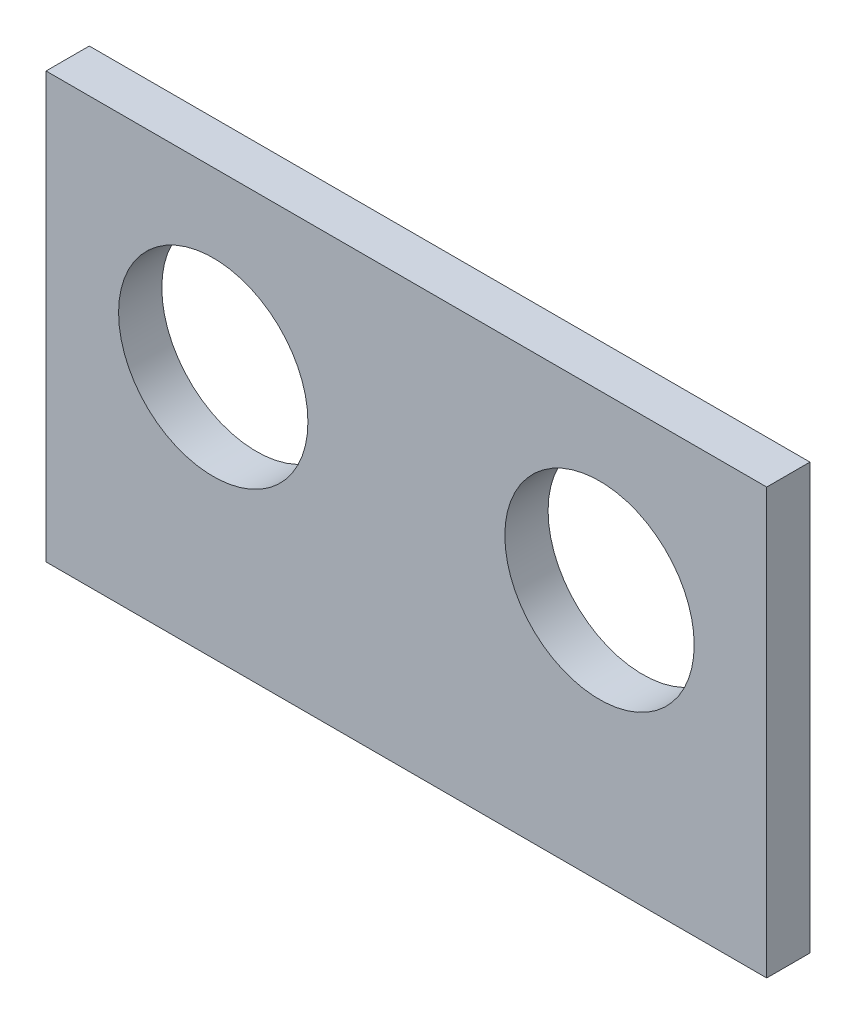
SolidWorks part; units mm, degrees
ref_plane "Front Plane" through (0, 0, 0) normal (0, 0, 1) x (1, 0, 0)
ref_plane "Top Plane" through (0, 0, 0) normal (0, 1, 0) x (1, 0, 0)
ref_plane "Right Plane" through (0, 0, 0) normal (1, 0, 0) x (0, 0, -1)
sketch "Sketch1" plane through (0, 0, 0) normal (0, 0, 1) x (1, 0, 0)
  line L0 (-6.7, 1.375) -> (6.7, 1.375) construction
  line L1 (-12.5, -7.375) -> (12.5, -7.375)
  line L2 (-12.5, -7.375) -> (-12.5, 7.375)
  line L3 (-12.5, 7.375) -> (12.5, 7.375)
  line L4 (12.5, -7.375) -> (12.5, 7.375)
  line L5 (-12.5, -7.375) -> (12.5, 7.375) construction
  line L6 (-12.5, 7.375) -> (12.5, -7.375) construction
  line L7 (-12.5, 1.375) -> (12.5, 1.375) construction
  line L8 (-6.7, -4.875) -> (-6.7, -7.375) construction
  line L9 (0, 7.375) -> (0, -7.375) construction
  circle A0 centre (-6.7, 1.375) radius 6.25
  circle A1 centre (6.7, 1.375) radius 6.25
  point P4 (0, 0)
  point P18 (0, 1.375)
  dimension "D1" = 12.5
  dimension "D2" = 13.4
  dimension "D3" = 6
  dimension "D4" = 25
  dimension "D5" = 2.5
extrude "Boss-Extrude1" add sketch "Sketch1" along normal blind 1.5 contours L3 A1 A0 L2 L1 L4 | L3 A0 | A1 L4 L3 | A0 L3 L2 | L3 A1 L4
sketch "Sketch2" plane through (0, 0, 1.5) normal (0, 0, 1) x (1, 0, 0)
  line L1 (-9.09, -5.265) -> (9.09, -5.265) construction
  line L2 (-9.09, -5.265) -> (-9.09, -6.935) construction
  line L3 (-9.09, -6.935) -> (9.09, -6.935) construction
  line L4 (9.09, -5.265) -> (9.09, -6.935) construction
  line L5 (-9.09, -5.265) -> (9.09, -6.935) construction
  line L6 (-9.09, -6.935) -> (9.09, -5.265) construction
  point P4 (0, -6.1)
sketch "Sketch3" plane through (0, 0, 0) normal (0, 0, -1) x (-1, 0, 0)
  circle A0 centre (-6.7, 1.375) radius 3.2843
  circle A1 centre (6.7, 1.375) radius 3.2843
  dimension "D1" = 6.5686
extrude "Cut-Extrude1" cut sketch "Sketch3" against normal blind 10
